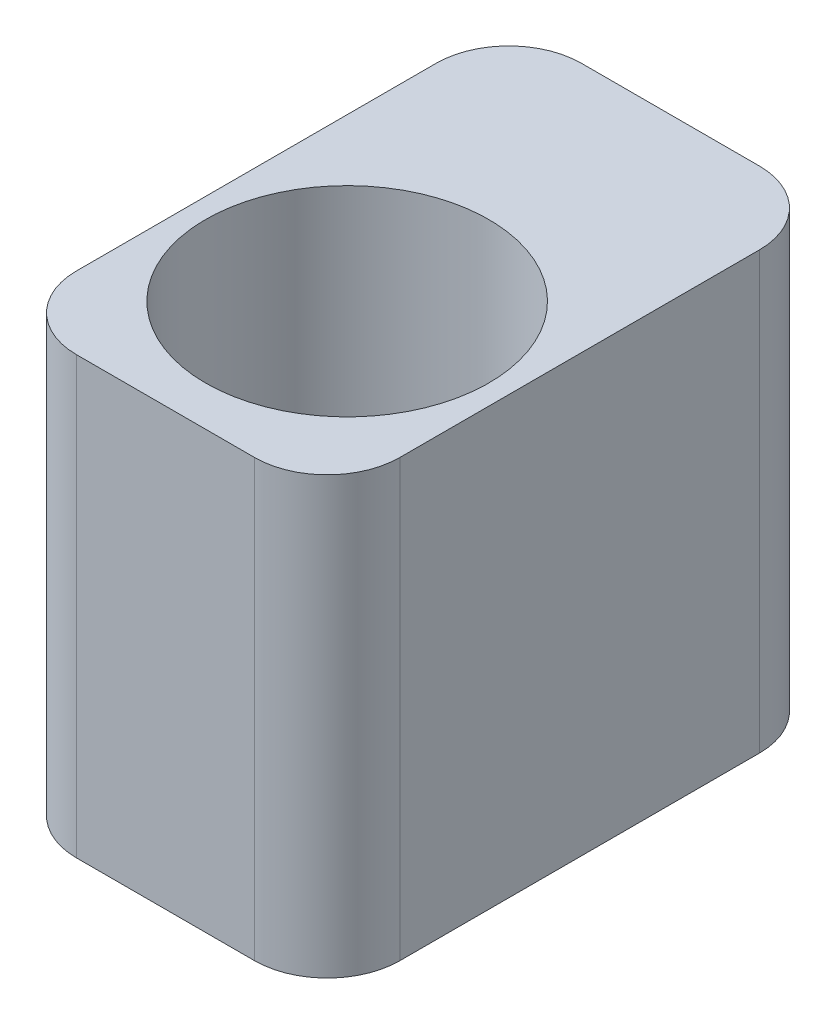
SolidWorks part; units mm, degrees
ref_plane "前视基准面" through (0, 0, 0) normal (0, 0, 1) x (1, 0, 0)
ref_plane "上视基准面" through (0, 0, 0) normal (0, 1, 0) x (1, 0, 0)
ref_plane "右视基准面" through (0, 0, 0) normal (1, 0, 0) x (0, 0, -1)
sketch "草图1" plane through (0, 0, 0) normal (0, 1, 0) x (1, 0, 0)
  line L1 (-22.25, 22.25) -> (22.25, 22.25)
  line L2 (-22.25, 22.25) -> (-22.25, -22.25)
  line L3 (-22.25, -22.25) -> (22.25, -22.25) construction
  line L4 (22.25, 22.25) -> (22.25, -22.25)
  line L5 (0, -22.25) -> (0, 22.25) construction
  line L6 (-22.25, 0) -> (22.25, 0) construction
  line L7 (-22.25, -22.25) -> (22.25, -22.25) construction
  line L8 (-22.25, -22.25) -> (-22.25, -47.25)
  line L9 (-22.25, -47.25) -> (22.25, -47.25)
  line L10 (22.25, -22.25) -> (22.25, -47.25)
  circle A1 centre (0, -22.25) radius 19.5
  point P0 (0, 0)
  dimension "D3" = 39
  dimension "D1" = 44.5
  dimension "D2" = 44.5
  dimension "D4" = 25
extrude "凸台-拉伸1" add sketch "草图1" along normal blind 60
fillet "圆角1" radius 10 4 edges at (-22.25, 30, 47.25) (22.25, 30, 47.25) (22.25, 30, -22.25) (-22.25, 30, -22.25)
